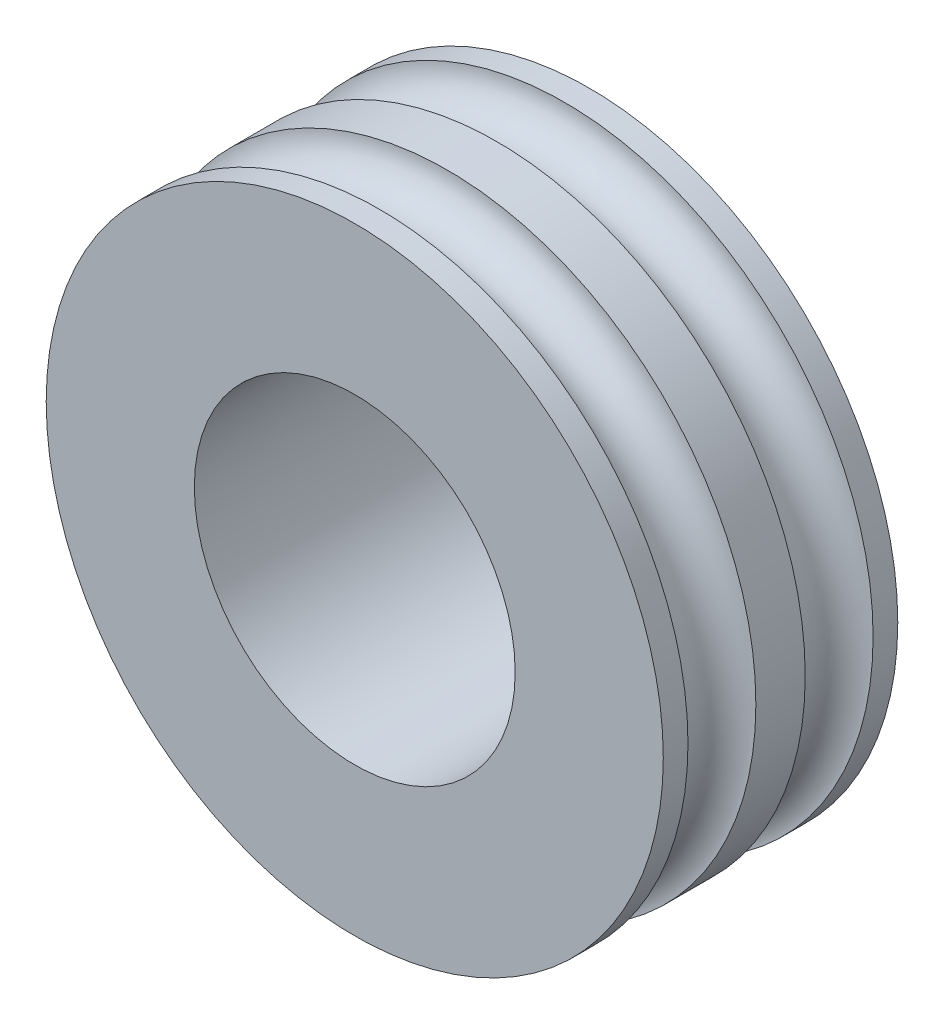
SolidWorks part; units mm, degrees
ref_plane "Front Plane" through (0, 0, 0) normal (0, 0, 1) x (1, 0, 0)
ref_plane "Top Plane" through (0, 0, 0) normal (0, 1, 0) x (1, 0, 0)
ref_plane "Right Plane" through (0, 0, 0) normal (1, 0, 0) x (0, 0, -1)
sketch "Sketch2" plane through (0, 0, 0) normal (1, 0, 0) x (0, 0, -1)
  line L0 (0.9, 2.6) -> (0.9, 5)
  line L1 (0.9, 5) -> (0.5, 5)
  line L2 (-1, 5) -> (-1, 2.6)
  line L4 (-1, 2.6) -> (0.9, 2.6)
  line L5 (-3.0147, 0) -> (3.0268, 0) construction
  line L6 (-0.6, 5) -> (-1, 5)
  arc A0 (-0.6, 5) -> (0.5, 5) centre (-0.05, 5) ccw
  dimension "D2" = 1.9
  dimension "D4" = 0.4
  dimension "D5" = 0.4
revolve "Revolve1" add sketch "Sketch2" angle 360 about L5
ref_plane "Plane1" through (0, 0, -0.9) normal (0, 0, -1) x (-1, 0, 0)
mirror "Mirror2" about plane through (0, 0, -0.9) normal (0, 0, -1) of "Revolve1"
